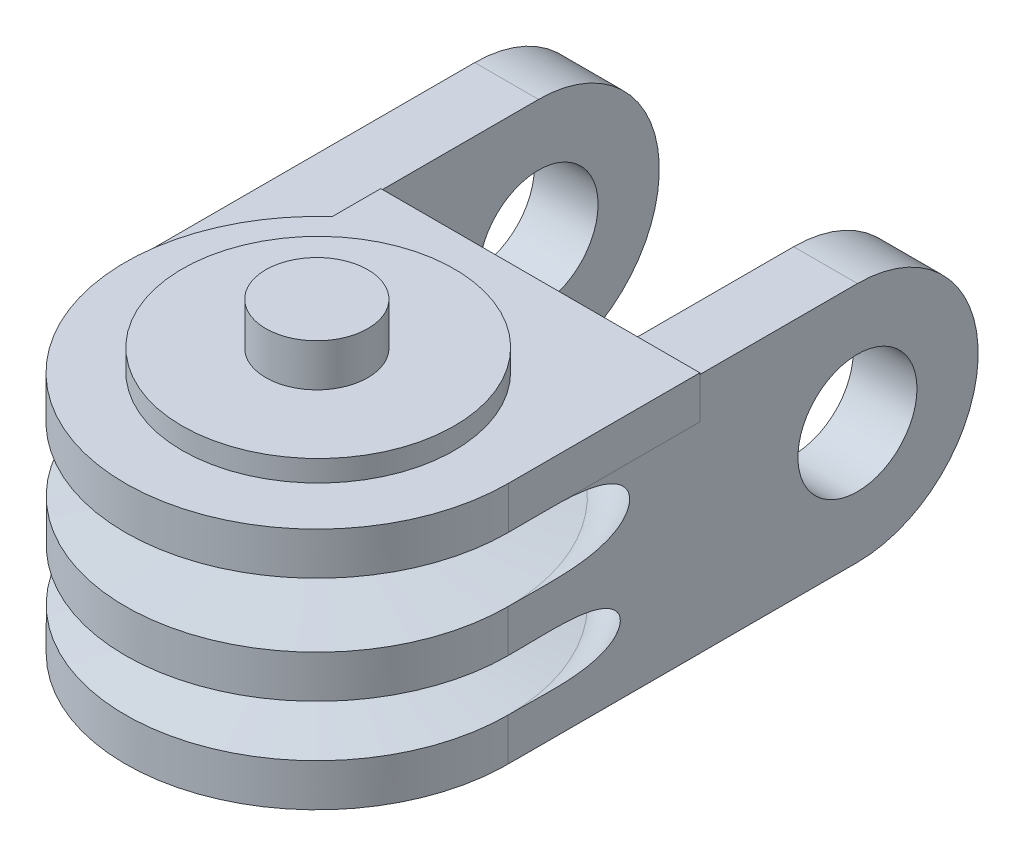
SolidWorks part; units mm, degrees
material "ABS"
ref_plane "Front Plane" through (0, 0, 0) normal (0, 0, 1) x (1, 0, 0)
ref_plane "Top Plane" through (0, 0, 0) normal (0, 1, 0) x (1, 0, 0)
ref_plane "Right Plane" through (0, 0, 0) normal (1, 0, 0) x (0, 0, -1)
sketch "Sketch3" plane through (0, 0, 0) normal (1, 0, 0) x (0, 0, -1)
  line L1 (-0.0671, -0.4347) -> (-0.0671, -9.2992)
  line L3 (-9.0671, 5.1207) -> (-4.0671, 5.6005)
  line L4 (-4.0671, 5.6005) -> (-4.0671, 7.6005)
  line L5 (-4.0671, 7.6005) -> (-9.0757, 8.1396)
  line L6 (-9.0757, 8.1396) -> (-9.0757, 10.1396)
  line L10 (-2.4671, 18.1396) -> (-0.0671, 18.1396)
  line L11 (-0.0671, 3.8562) -> (-0.0671, 18.1396)
  line L12 (-0.0671, 3.8562) -> (-0.0671, -0.4347)
  line L19 (-2.4671, -1.2992) -> (-2.4671, -9.2992)
  line L23 (-2.4671, 10.1396) -> (-2.4671, 18.1396)
  line L26 (-2.4671, -9.2992) -> (-0.0671, -9.2992)
  line L27 (-2.4671, 10.1396) -> (-9.0757, 10.1396)
  line L28 (-9.0671, -1.2992) -> (-9.0671, 0.7008)
  line L29 (-9.0671, 0.7008) -> (-4.0671, 1.544)
  line L30 (-4.0671, 1.544) -> (-4.0671, 2.544)
  line L31 (-4.0671, 2.544) -> (-9.0671, 3.1207)
  line L32 (-9.0671, 5.1207) -> (-9.0671, 3.1207)
  line L33 (-0.0671, -0.4347) -> (-0.0671, -9.2992) construction
  line L34 (-9.0671, -1.2992) -> (-2.4671, -1.2992)
  line L35 (-9.3178, 2.8658) -> (5.0075, 2.8658) construction
  dimension "D2" = 8
  dimension "D3" = 2.4
  dimension "D4" = 4
  dimension "D5" = 4
  dimension "D6" = 9
  dimension "D7" = 9
  dimension "D8" = 2
  dimension "D9" = 1
  dimension "D10" = 2
  dimension "D11" = 90
  dimension "D12" = 90
  dimension "D13" = 2.4
  dimension "D14" = 90
  dimension "D15" = 90
  dimension "D16" = 90
  dimension "D17" = 90
  dimension "D18" = 90
  dimension "D19" = 8
  dimension "D20" = 2
  dimension "D21" = 2
revolve "Revolve1" add sketch "Sketch3" angle 360 about L12
ref_plane "Plane5" through (0, 10.1396, 0) normal (0, 1, 0) x (1, 0, 0)
ref_plane "Plane6" through (0, -1.2992, 0) normal (0, -1, 0) x (-1, 0, 0)
ref_plane "Plane7" through (-6, 0, 0) normal (1, 0, 0) x (0, 0, -1)
sketch "Sketch4" plane through (0, 10.1396, 0) normal (0, 1, 0) x (1, 0, 0)
  circle A1 centre (0, 0) radius 6.4
  circle A2 centre (0, -0.0671) radius 2
  circle A4 centre (0, -0.0671) radius 2
  dimension "D1" = 0.4
sketch "Sketch5" plane through (-6, 0, 3.8542) normal (1, 0, 0) x (0, 0, -1)
  line L0 (20.2157, 10.0617) -> (3.7871, 10.0617)
  line L3 (3.7871, 3.8562) -> (3.7871, 18.1396) construction
  line L4 (3.7871, 10.0617) -> (3.7871, -1.2956)
  line L5 (12.7957, 8.1396) -> (12.7957, 10.1396) construction
  line L11 (3.7871, -1.2956) -> (20.2157, -1.2956)
  arc A1 (20.2157, -1.2956) -> (20.2157, 10.0617) centre (20.2157, 4.383) ccw
  circle A3 centre (20.2157, 4.383) radius 2.8
  dimension "D1" = 7.42
extrude "Boss-Extrude3" add sketch "Sketch4" along normal blind 1 separate body
extrude "Boss-Extrude6" add sketch "Sketch5" against normal blind 3 and the other way blind 0.0001
mirror "Mirror1" about plane through (0, 0, 0) normal (1, 0, 0) of "Boss-Extrude6"
sketch "Sketch9" plane through (0, -1.2992, 0) normal (0, -1, 0) x (-1, 0, 0)
  circle A17 centre (0, 0) radius 2.4
  circle A18 centre (0, 0) radius 2
  circle A19 centre (0, 0) radius 6.419
sketch "Sketch11" plane through (0, 0, 0) normal (1, 0, 0) x (0, 0, -1)
  line L28 (-2.4671, -1.2992) -> (-2.4671, -9.2992)
  line L30 (-2.4671, -9.2992) -> (-0.0671, -9.2992)
  line L36 (-0.0671, -9.2992) -> (-0.0671, -0.4347)
  line L40 (-0.0671, -0.4347) -> (-0.0671, 3.8562)
  line L66 (-0.0671, 3.8562) -> (-0.0671, 18.1396)
  line L67 (-0.0671, 18.1396) -> (-2.4671, 18.1396)
  line L68 (-2.4671, 18.1396) -> (-2.4671, 10.1396)
  line L69 (-2.4671, 10.1396) -> (-9.0757, 10.1396)
  line L70 (-9.0757, 10.1396) -> (-9.0757, 8.1396)
  line L74 (-9.0757, 8.1396) -> (-4.0671, 7.6005)
  line L75 (-4.0671, 7.6005) -> (-4.0671, 5.6005)
  line L76 (-4.0671, 5.6005) -> (-9.0671, 5.1207)
  line L77 (-9.0671, 5.1207) -> (-9.0671, 3.1207)
  line L79 (-9.0671, 3.1207) -> (-4.0671, 2.544)
  line L80 (-4.0671, 2.544) -> (-4.0671, 1.544)
  line L81 (-4.0671, 1.544) -> (-9.0671, 0.7008)
  line L82 (-9.0671, 0.7008) -> (-9.0671, -1.2992)
  line L83 (-9.0671, -1.2992) -> (-2.4671, -1.2992)
  line L89 (-0.0671, 18.1396) -> (-2.4671, 18.1396)
  line L93 (-9.0757, 8.1396) -> (-4.0671, 7.6005)
  line L94 (-4.0671, 7.6005) -> (-4.0671, 5.6005)
  line L95 (-4.0671, 5.6005) -> (-9.0671, 5.1207)
  line L97 (-9.0671, 3.1207) -> (-4.0671, 2.544)
  line L98 (-4.0671, 2.544) -> (-4.0671, 1.544)
  line L99 (-4.0671, 1.544) -> (-9.0671, 0.7008)
  arc A4 (-9.0671, 5.1207) -> (-9.0757, 8.1396) centre (-9.2119, 6.6297) cw
  arc A5 (-9.0671, 0.7008) -> (-9.0671, 3.1207) centre (-9.2712, 1.9108) cw
  dimension "D1" = 0
sketch "Sketch17" plane through (0, 10.1396, 0) normal (0, 1, 0) x (1, 0, 0)
  line L0 (-5.9999, 6.6527) -> (-5.9999, 16.3615) construction
  line L8 (-5.9999, 6.6527) -> (-5.9999, 8.9415)
  line L16 (0, 8.9415) -> (-5.9999, 8.9415)
  line L17 (9.0086, -0.0671) -> (9.0086, 8.9415)
  line L18 (0, 8.9415) -> (9.0086, 8.9415)
  circle A0 centre (0, -0.0671) radius 9.0086 construction
  arc A1 (0, 8.9415) -> (-5.9999, 6.6527) centre (0, -0.0671) ccw
  arc A6 (9.0086, -0.0671) -> (0, 8.9415) centre (0, -0.0671) ccw
  circle M8 centre (0, -0.0671) radius 9.0086
extrude "Boss-Extrude10" add sketch "Sketch17" against normal blind 2 contours L18 L17 M8 | L16 L8 M8
sketch "Sketch18" plane through (0, -1.2992, 0) normal (0, -1, 0) x (1, 0, 0)
  line L1 (-6, 0.0671) -> (-1.014, -8.2015)
  line L3 (-6, -12.65) -> (-6, 12.65) construction
  line L4 (8.9999, -8.9415) -> (8.9999, -0.3286)
  line L5 (0, -8.9415) -> (8.9999, -8.9415)
  line L8 (9, 0.0671) -> (-9, 0.0671) construction
  line L9 (-6, 0.0671) -> (-6, -8.9415)
  line L10 (-6, -8.9415) -> (0, -8.9415)
  line L11 (-1.014, -8.2015) -> (0.7763, -8.2015)
  line L12 (0.7763, -8.2015) -> (8.9999, -0.3286)
extrude "Boss-Extrude22" add sketch "Sketch18" against normal blind 2
extrude "Boss-Extrude9" add sketch "Sketch9" along normal blind 1
revolve "Cut-Revolve3" cut sketch "Sketch11" angle 360 about L1
sketch "Sketch13" plane through (0, 11.1396, 0) normal (0, 1, 0) x (1, 0, 0)
  arc A0 (6.4, -5.4) -> (4.4945, 7.0654) centre (0, 0) ccw
  arc A1 (-4.4945, 7.0654) -> (-6.4, -5.4) centre (0, 0) ccw
sketch "Sketch20" plane through (9, 0, 0) normal (1, 0, 0) x (0, 0, -1)
  line L0 (-6.419, -2.2992) -> (6.419, -2.2992) construction
  line L1 (-4.1937, 19.2941) -> (3.8063, 19.2941)
  line L2 (-4.1937, 19.2941) -> (-4.1937, 13.1396)
  line L3 (-4.1937, 13.1396) -> (3.8063, 13.1396)
  line L4 (3.8063, 19.2941) -> (3.8063, 13.1396)
  line L5 (-4.4042, -4.2992) -> (3.5958, -4.2992)
  line L6 (-4.4042, -4.2992) -> (-4.4042, -9.6829)
  line L7 (-4.4042, -9.6829) -> (3.5958, -9.6829)
  line L8 (3.5958, -4.2992) -> (3.5958, -9.6829)
  line L9 (6.4, 11.1396) -> (-6.4, 11.1396) construction
  dimension "D1" = 8
  dimension "D2" = 8
  dimension "D3" = 2
  dimension "D4" = 2
extrude "Cut-Extrude5" cut sketch "Sketch20" against normal up to surface (18 mm away) up to face at (-9, 4.383, -19.1615)
sketch "Sketch21" plane through (-9, 0, 0) normal (-1, 0, 0) x (0, 0, 1)
  line L0 (-16.3615, 4.383) -> (-23.5435, 4.383) construction
  line L1 (-16.3615, 15.8382) -> (-16.3615, -3.042) construction
  line L2 (-16.3615, 4.383) -> (-10.8026, 4.383) construction
  line L3 (0.0671, -4.2992) -> (0.0671, 9.9513) construction
  line L4 (-2.3329, -4.2992) -> (2.4671, -4.2992) construction
  line L5 (0.0671, 3.8562) -> (0.0671, 18.1396) construction
equation "\"toler\"= 0.4mm"
